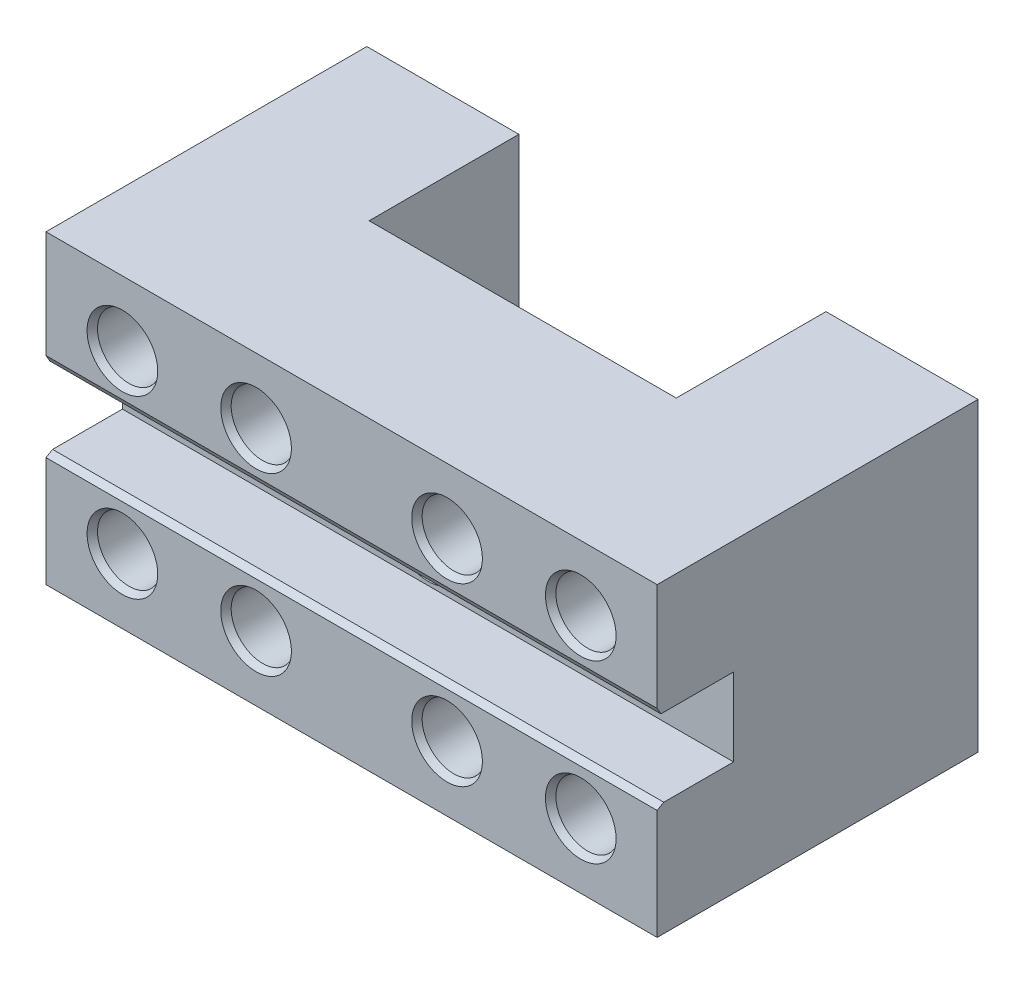
SolidWorks part; units mm, degrees
ref_plane "Спереди" through (0, 0, 0) normal (0, 0, 1) x (1, 0, 0)
ref_plane "Сверху" through (0, 0, 0) normal (0, 1, 0) x (1, 0, 0)
ref_plane "Справа" through (0, 0, 0) normal (1, 0, 0) x (0, 0, -1)
sketch "Sketch2" plane through (0, 0, 0) normal (0, 1, 0) x (1, 0, 0)
  line L0 (-31.3121, 30) -> (-31.3121, 0)
  line L1 (-31.3121, 0) -> (48.6879, 0)
  line L2 (48.6879, 0) -> (48.6879, 30)
  line L3 (48.6879, 30) -> (28.7879, 30)
  line L4 (28.7879, 30) -> (28.7879, 10.4)
  line L5 (28.7879, 10.4) -> (-11.4121, 10.4)
  line L6 (-11.4121, 10.4) -> (-11.4121, 30)
  line L7 (-11.4121, 30) -> (-31.3121, 30)
  dimension "D1" = 80
  dimension "D2" = 40.2
  dimension "D3" = 30
  dimension "D4" = 19.6
extrude "Boss-Extrude2" add sketch "Sketch2" along normal blind 40
sketch "Sketch4" plane through (48.6879, 0, 0) normal (1, 0, 0) x (0, 0, -1)
  line L0 (0, 0) -> (-12, 0)
  line L1 (-12, 0) -> (-12, 14.9)
  line L2 (-12, 14.9) -> (-2, 14.9)
  line L3 (-2, 14.9) -> (-2, 25.1)
  line L4 (-2, 25.1) -> (-12, 25.1)
  line L5 (-12, 25.1) -> (-12, 40)
  line L6 (-12, 40) -> (0, 40)
  line L7 (0, 40) -> (0, 0)
  dimension "D1" = 10.2
  dimension "D2" = 12
  dimension "D3" = 10
extrude "Boss-Extrude3" add sketch "Sketch4" against normal up to surface (80 mm away) up to face at (-31.3121, 20, -15)
sketch "Sketch5" plane through (0, 0, 12) normal (0, 0, 1) x (1, 0, 0)
  line L0 (8.6879, 40) -> (8.6879, 0) construction
  line L1 (-31.3121, 40) -> (48.6879, 40) construction
  line L2 (-31.3121, 0) -> (48.6879, 0) construction
  line L4 (21.1879, 8.5) -> (-3.8121, 8.5) construction
  line L5 (21.1879, 8.5) -> (21.1879, 31.5) construction
  line L6 (21.1879, 31.5) -> (-3.8121, 31.5) construction
  line L7 (-3.8121, 8.5) -> (-3.8121, 31.5) construction
  line L8 (21.1879, 8.5) -> (-3.8121, 31.5) construction
  line L9 (21.1879, 31.5) -> (-3.8121, 8.5) construction
  line L10 (38.6879, 8.5) -> (-21.3121, 8.5) construction
  line L11 (38.6879, 8.5) -> (38.6879, 31.5) construction
  line L12 (38.6879, 31.5) -> (-21.3121, 31.5) construction
  line L13 (-21.3121, 8.5) -> (-21.3121, 31.5) construction
  line L14 (38.6879, 8.5) -> (-21.3121, 31.5) construction
  line L15 (38.6879, 31.5) -> (-21.3121, 8.5) construction
  circle A0 centre (-3.8121, 31.5) radius 4.125
  circle A1 centre (21.1879, 31.5) radius 4.125
  circle A2 centre (21.1879, 8.5) radius 4.125
  circle A3 centre (-3.8121, 8.5) radius 4.125
  circle A4 centre (-21.3121, 31.5) radius 4.125
  circle A5 centre (-21.3121, 8.5) radius 4.125
  circle A6 centre (38.6879, 8.5) radius 4.125
  circle A7 centre (38.6879, 31.5) radius 4.125
  circle A8 centre (8.6879, 20) radius 4.125
  point P6 (8.6879, 20)
  point P15 (8.6879, 20)
  dimension "D2" = 8.25
  dimension "D1" = 25
  dimension "D3" = 23
  dimension "D4" = 60
extrude "Cut-Extrude1" cut sketch "Sketch5" against normal through all
chamfer "Chamfer1" distance 0.5 angle 60 11 edges at (42.8129, 8.5, 12) (42.8129, 31.5, 12) (25.3129, 8.5, 12) (25.3129, 31.5, 12) (0.3129, 31.5, 12) (12.8129, 20, 2) (0.3129, 8.5, 12) (-17.1871, 8.5, 12) (-17.1871, 31.5, 12) (8.6879, 25.1, 12) (8.6879, 14.9, 12)
